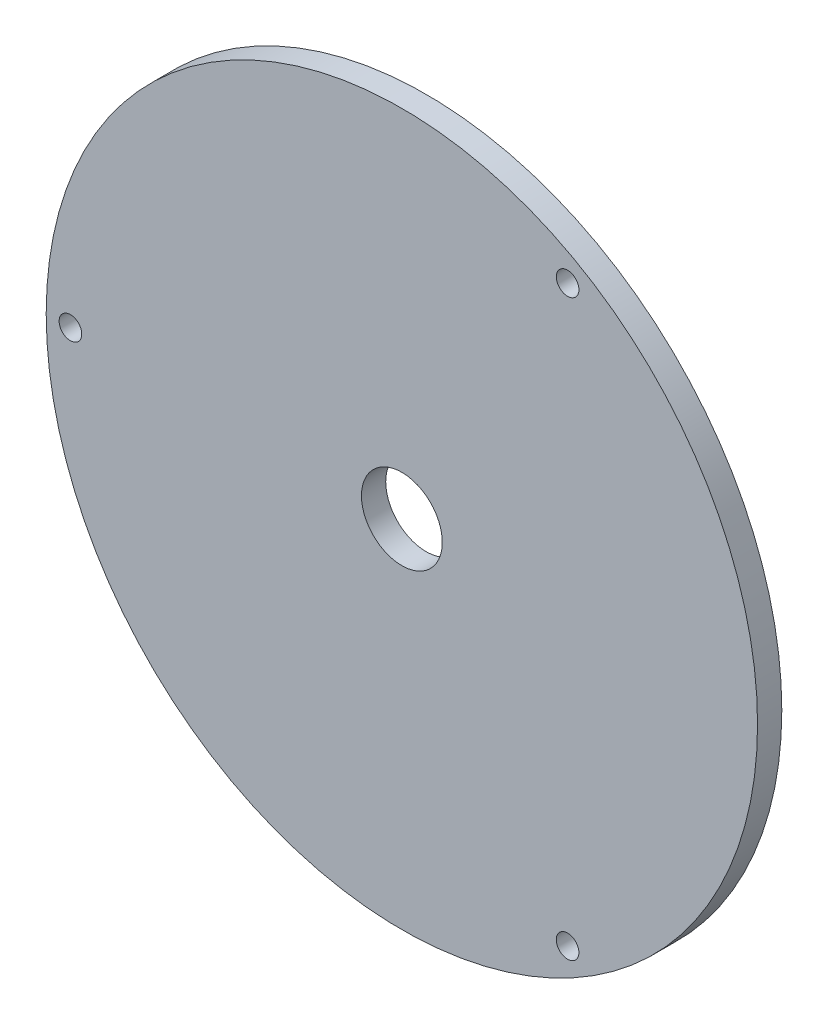
SolidWorks part; units mm, degrees
ref_plane "前视基准面" through (0, 0, 0) normal (0, 0, 1) x (1, 0, 0)
ref_plane "上视基准面" through (0, 0, 0) normal (0, 1, 0) x (1, 0, 0)
ref_plane "右视基准面" through (0, 0, 0) normal (1, 0, 0) x (0, 0, -1)
sketch "草图2" plane through (0, 0, 0) normal (0, 0, 1) x (1, 0, 0)
  line L1 (-6, -20.3) -> (6, -20.3)
  line L2 (6, -20.3) -> (7.4798, -16.1522)
  line L3 (-6, -20.3) -> (-7.4798, -16.1522)
  arc A0 (7.4798, -16.1522) -> (-7.4798, -16.1522) centre (0, 0) ccw
extrude "凸台-拉伸1" add sketch "草图2" along normal blind 1.5
sketch "草图3" plane through (0, 0, 1.5) normal (0, 0, 1) x (1, 0, 0)
  circle A0 centre (0, 0) radius 22
extrude "凸台-拉伸2" add sketch "草图3" along normal blind 1.5
sketch "草图4" plane through (0, 0, 0) normal (0, 0, -1) x (-1, 0, 0)
  circle A0 centre (0, 0) radius 35.0705
extrude "切除-拉伸1" cut sketch "草图4" against normal blind 1.5
sketch "草图5" plane through (0, 0, 1.5) normal (0, 0, -1) x (-1, 0, 0)
  line L0 (0, 0) -> (20.5, 0) construction
  circle A6 centre (20.5, 0) radius 0.7
  circle A7 centre (-10.25, -17.7535) radius 0.7
  circle A8 centre (-10.25, 17.7535) radius 0.7
  dimension "D1" = 3
  dimension "D2" = 20.5
extrude "切除-拉伸2" cut sketch "草图5" against normal blind 1.5
sketch "草图6" plane through (0, 0, 1.5) normal (0, 0, -1) x (-1, 0, 0)
  circle A0 centre (0, 0) radius 2.5
extrude "切除-拉伸3" cut sketch "草图6" against normal blind 1.5
